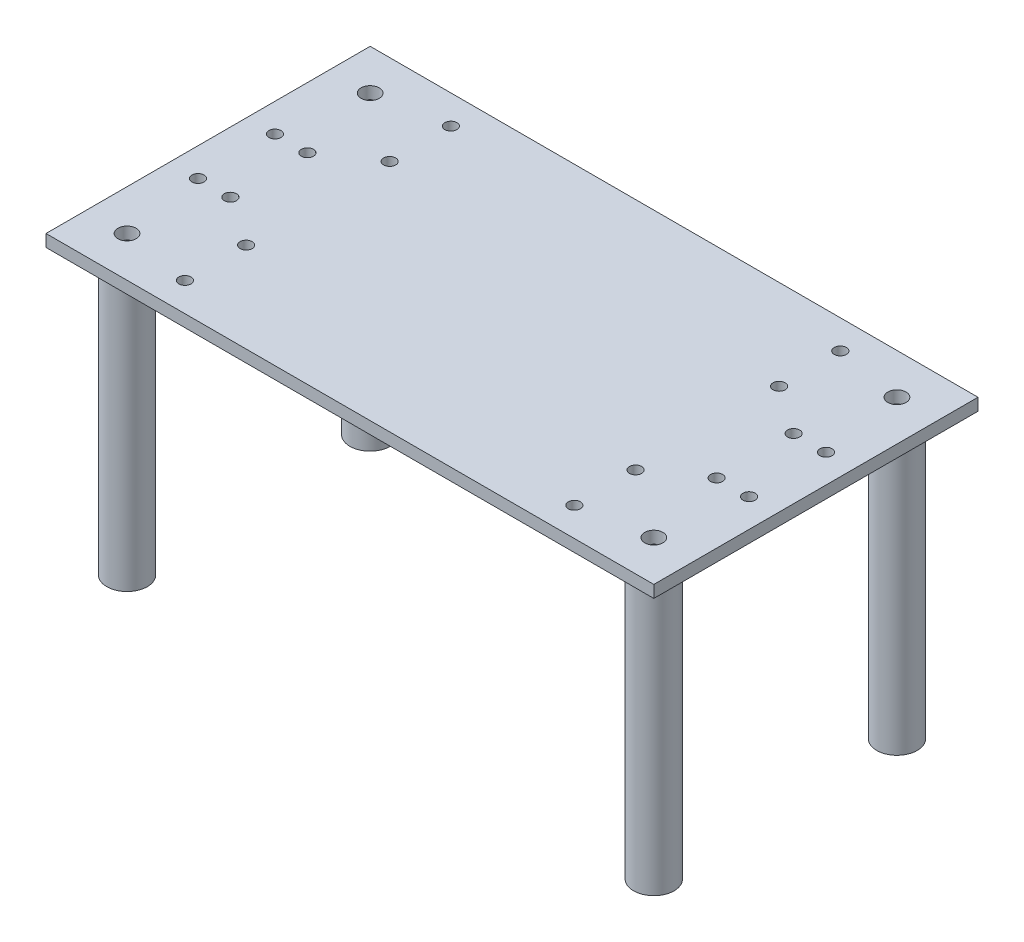
SolidWorks part; units mm, degrees
ref_plane "Front Plane" through (0, 0, 0) normal (0, 0, 1) x (1, 0, 0)
ref_plane "Top Plane" through (0, 0, 0) normal (0, 1, 0) x (1, 0, 0)
ref_plane "Right Plane" through (0, 0, 0) normal (1, 0, 0) x (0, 0, -1)
sketch "Sketch2" plane through (0, 0, 0) normal (0, 1, 0) x (1, 0, 0)
  line L0 (-83.4647, 1.8257) -> (66.5353, 1.8257)
  line L1 (-83.4647, 41.8257) -> (66.5353, 41.8257)
  line L2 (-83.4647, 41.8257) -> (-83.4647, -38.1743)
  line L3 (-83.4647, -38.1743) -> (66.5353, -38.1743)
  line L4 (66.5353, 41.8257) -> (66.5353, -38.1743)
  circle A0 centre (-68.4647, 11.3257) radius 1.5
  circle A1 centre (-68.4647, -7.6743) radius 1.5
  circle A2 centre (-76.4647, 11.3257) radius 1.5
  circle A3 centre (-76.4647, -7.6743) radius 1.5
  circle A4 centre (51.5353, -7.6743) radius 1.5
  circle A5 centre (59.5353, -7.6743) radius 1.5
  circle A6 centre (59.5353, 11.3257) radius 1.5
  circle A7 centre (51.5353, 11.3257) radius 1.5
  dimension "D3" = 3
  dimension "D7" = 3
  dimension "D1" = 80
  dimension "D2" = 150
  dimension "D4" = 19
  dimension "D5" = 15
  dimension "D6" = 9.5
  dimension "D8" = 7
  dimension "D9" = 7
  dimension "D10" = 15
extrude "Boss-Extrude1" add sketch "Sketch2" against normal blind 3 contours L4 L0 L2 L3 A3 A1 | L4 L1 L2 L0 A2 A0
sketch "Sketch3" plane through (0, 0, 0) normal (0, 1, 0) x (1, 0, 0)
  line L0 (-83.4647, 41.8257) -> (-83.4647, -38.1743) construction
  line L1 (-83.4647, 41.8257) -> (66.5353, 41.8257) construction
  line L2 (-83.4647, -38.1743) -> (66.5353, -38.1743) construction
  line L3 (66.5353, 41.8257) -> (66.5353, -38.1743) construction
  circle A4 centre (56.5353, 31.8257) radius 2.25
  circle A5 centre (56.5353, -28.1743) radius 2.25
  circle A6 centre (-73.4647, -28.1743) radius 2.25
  circle A7 centre (-73.4647, 31.8257) radius 2.25
  dimension "D11" = 4.5
  dimension "D12" = 4.5
  dimension "D13" = 4.5
  dimension "D2" = 10
  dimension "D3" = 10
  dimension "D4" = 10
  dimension "D5" = 10
  dimension "D6" = 10
  dimension "D7" = 10
  dimension "D8" = 10
  dimension "D9" = 10
sketch "Sketch5" plane through (0, -3, 0) normal (0, -1, 0) x (1, 0, 0)
  line L0 (-83.4647, -41.8257) -> (-83.4647, 38.1743) construction
  line L1 (-83.4647, 38.1743) -> (66.5353, 38.1743) construction
  line L2 (-83.4647, -41.8257) -> (66.5353, -41.8257) construction
  line L3 (66.5353, -41.8257) -> (66.5353, 38.1743) construction
  circle A0 centre (-73.4647, 28.1743) radius 5
  circle A1 centre (56.5353, 28.1743) radius 5
  circle A2 centre (56.5353, -31.8257) radius 5
  circle A3 centre (-73.4647, -31.8257) radius 5
  circle A4 centre (56.5353, 28.1743) radius 2.5
  circle A5 centre (56.5353, -31.8257) radius 2.5
  circle A6 centre (-73.4647, -31.8257) radius 2.5
  circle A7 centre (-73.4647, 28.1743) radius 2.5
  dimension "D1" = 10
  dimension "D10" = 5
  dimension "D2" = 10
  dimension "D3" = 10
  dimension "D4" = 10
  dimension "D5" = 10
  dimension "D6" = 10
  dimension "D7" = 10
  dimension "D8" = 10
  dimension "D9" = 10
extrude "Boss-Extrude3" add sketch "Sketch5" along normal blind 70
sketch "Sketch7" plane through (0, 0, 0) normal (0, 1, 0) x (1, 0, 0)
  circle A0 centre (-56.4498, 34.7247) radius 1.5
  circle A1 centre (-56.4498, 19.6208) radius 1.5
  circle A2 centre (39.6553, 34.7247) radius 1.5
  circle A3 centre (39.6553, 19.6208) radius 1.5
  circle A4 centre (-56.2843, -15.9694) radius 1.5
  circle A5 centre (-56.2843, -31.0732) radius 1.5
  circle A6 centre (39.8208, -15.9694) radius 1.5
  circle A7 centre (39.8208, -31.0732) radius 1.5
extrude "Cut-Extrude1" cut sketch "Sketch7" against normal blind 10
extrude "Cut-Extrude2" cut sketch "Sketch3" against normal blind 5
